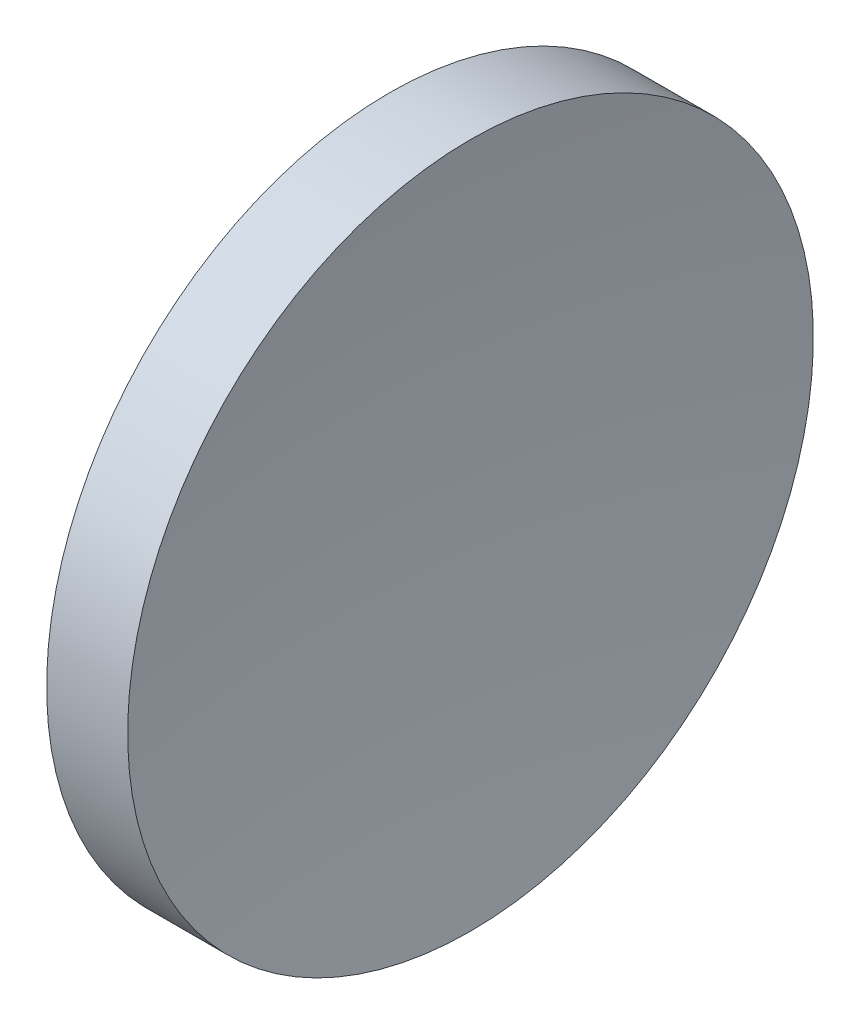
SolidWorks part; units mm, degrees
ref_plane "前视基准面" through (0, 0, 0) normal (0, 0, 1) x (1, 0, 0)
ref_plane "上视基准面" through (0, 0, 0) normal (0, 1, 0) x (1, 0, 0)
ref_plane "右视基准面" through (0, 0, 0) normal (1, 0, 0) x (0, 0, -1)
sketch "草图1" plane through (0, 0, 0) normal (0, 0, 1) x (1, 0, 0)
  line L0 (55.0074, 32.5787) -> (64.0943, 32.5787) construction
  line L1 (57.3582, 32.5787) -> (57.3582, 45.0787)
  line L2 (59.3582, 32.5787) -> (57.3582, 32.5787)
  line L3 (57.3582, 45.0787) -> (60.312, 45.0787)
  arc A0 (60.312, 45.0787) -> (59.3582, 32.5787) centre (141.9782, 32.561) ccw
revolve "旋转1" add sketch "草图1" angle 360 about L0
